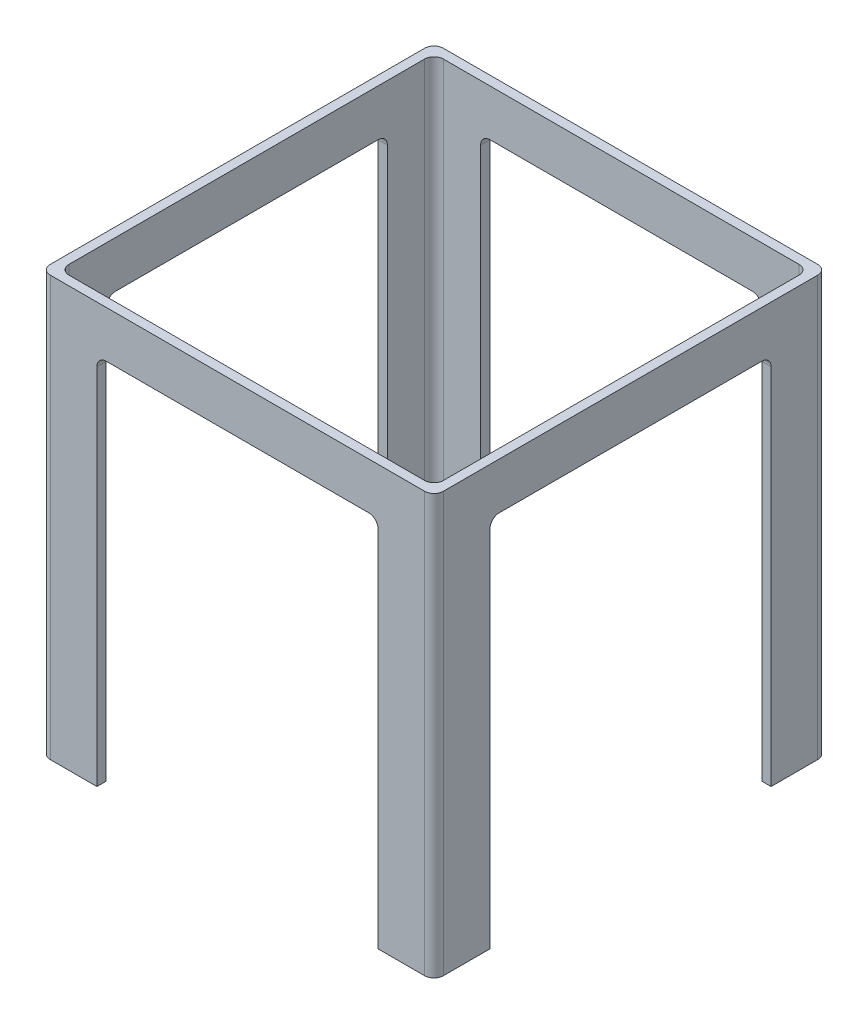
SolidWorks part; units mm, degrees
ref_plane "Front Plane" through (0, 0, 0) normal (0, 0, 1) x (1, 0, 0)
ref_plane "Top Plane" through (0, 0, 0) normal (0, 1, 0) x (1, 0, 0)
ref_plane "Right Plane" through (0, 0, 0) normal (1, 0, 0) x (0, 0, -1)
sketch "Sketch1" plane through (0, 0, 0) normal (0, 1, 0) x (1, 0, 0)
  line L0 (-42.15, 42.15) -> (42.15, 42.15)
  line L1 (-40, -40) -> (40, -40) construction
  line L2 (-40, -40) -> (-40, 40) construction
  line L3 (-40, 40) -> (40, 40) construction
  line L4 (40, -40) -> (40, 40) construction
  line L5 (-40, -40) -> (40, 40) construction
  line L6 (-40, 40) -> (40, -40) construction
  line L7 (-40.15, -40.15) -> (40.15, -40.15)
  line L8 (-40.15, -40.15) -> (-40.15, 40.15)
  line L9 (-40.15, 40.15) -> (40.15, 40.15)
  line L10 (40.15, -40.15) -> (40.15, 40.15)
  line L11 (-40.15, -40.15) -> (40.15, 40.15) construction
  line L12 (-40.15, 40.15) -> (40.15, -40.15) construction
  line L13 (42.15, -42.15) -> (42.15, 42.15)
  line L14 (-42.15, -42.15) -> (42.15, -42.15)
  line L15 (-42.15, -42.15) -> (-42.15, 42.15)
  point P0 (0, 0)
  point P6 (0, 0)
  dimension "D1" = 80
  dimension "D2" = 80
  dimension "D3" = 0.15
  dimension "D4" = 0.15
  dimension "D5" = 2
extrude "Boss-Extrude1" add sketch "Sketch1" along normal blind 10
sketch "Sketch2" plane through (0, 0, 0) normal (0, -1, 0) x (1, 0, 0)
  line L0 (-40.15, -40.15) -> (-40.15, 40.15) construction
  line L1 (-40.15, 40.15) -> (40.15, 40.15) construction
  line L2 (-40.15, -40.15) -> (-40.15, 40.15)
  line L3 (-40.15, 40.15) -> (40.15, 40.15)
  line L4 (-42.15, 42.15) -> (-42.15, -42.15)
  line L5 (-42.15, -42.15) -> (42.15, -42.15)
  line L6 (42.15, -42.15) -> (42.15, 42.15)
  line L7 (42.15, 42.15) -> (-42.15, 42.15)
  line L8 (-42.15, 42.15) -> (-42.15, -42.15)
  line L9 (-42.15, -42.15) -> (42.15, -42.15)
  line L10 (42.15, -42.15) -> (42.15, 42.15)
  line L11 (42.15, 42.15) -> (-42.15, 42.15)
  line L12 (-42.15, 30.15) -> (-40.15, 30.15)
  line L13 (-30.15, 42.15) -> (-30.15, 40.15)
  dimension "D2" = 10
  dimension "D3" = 10
extrude "Boss-Extrude2" add sketch "Sketch2" along normal blind 80
mirror "Mirror1" about plane through (0, 0, 0) normal (1, 0, 0) of "Boss-Extrude2"
mirror "Mirror2" about plane through (0, 0, 0) normal (0, 0, 1) of "Mirror1", "Boss-Extrude2"
fillet "Fillet1" radius 2 16 edges at (-42.15, -35, -42.15) (42.15, -35, -42.15) (42.15, -35, 42.15) (-42.15, -35, 42.15) (40.15, -35, 40.15) (-40.15, -35, 40.15) (-40.15, -35, -40.15) (40.15, -35, -40.15) (-41.15, 0, 30.15) (-41.15, 0, -30.15) (-30.15, 0, -41.15) (30.15, 0, -41.15) (41.15, 0, -30.15) (41.15, 0, 30.15) (30.15, 0, 41.15) (-30.15, 0, 41.15)
equation "\"BOTTLEOD1\"=80"
equation "\"BOTTLEOD2\"=80"
equation "\"D2@Sketch1\"=\"BOTTLEOD2\""
equation "\"D1@Sketch1\"=\"BOTTLEOD1\""
equation "\"C\"=0.15"
equation "\"D3@Sketch1\"=\"C\""
equation "\"D4@Sketch1\"=\"C\""
equation "\"T\"=2"
equation "\"D5@Sketch1\"=\"T\""
equation "\"H\"=10"
equation "\"D1@Boss-Extrude1\"=\"H\""
equation "\"F\"=2"
equation "\"D1@Fillet1\"=\"F\""
equation "\"FL\"=10"
equation "\"D3@Sketch2\"=\"FL\""
equation "\"D2@Sketch2\"=\"FL\""
equation "\"H2\"=80"
equation "\"D1@Boss-Extrude2\"=\"H2\""
